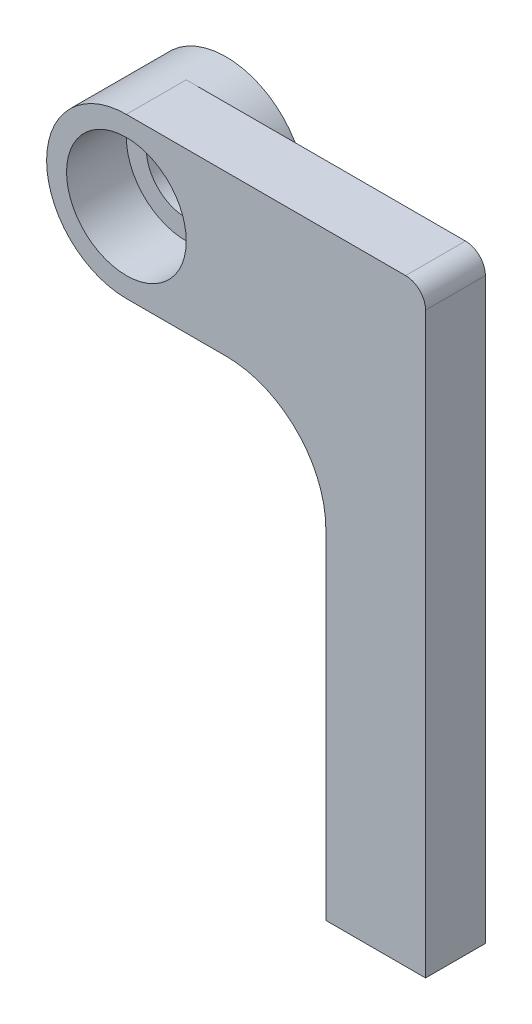
SolidWorks part; units mm, degrees
ref_plane "Front Plane" through (0, 0, 0) normal (0, 0, 1) x (1, 0, 0)
ref_plane "Top Plane" through (0, 0, 0) normal (0, 1, 0) x (1, 0, 0)
ref_plane "Right Plane" through (0, 0, 0) normal (1, 0, 0) x (0, 0, -1)
sketch "Sketch1" plane through (0, 0, 0) normal (0, 0, 1) x (1, 0, 0)
  line L1 (0, -4) -> (10, -4)
  line L3 (0, 4) -> (10, 4)
  line L6 (10, 4) -> (15, 4)
  line L7 (10, -4) -> (10, -26)
  line L8 (10, -26) -> (15, -26)
  line L9 (15, 4) -> (15, -26)
  arc A0 (0, 4) -> (0, -4) centre (0, 0) ccw
  circle A1 centre (0, 0) radius 2
  dimension "D1" = 8
  dimension "D2" = 4
  dimension "D4" = 5
  dimension "D3" = 10
  dimension "D5" = 30
extrude "Boss-Extrude1" add sketch "Sketch1" along normal blind 3 contours L3 L6 L9 L8 L7 L1 A0
sketch "Sketch2" plane through (0, 0, 0) normal (0, 0, -1) x (-1, 0, 0)
  circle A0 centre (0, 0) radius 3
extrude "Cut-Extrude1" cut sketch "Sketch2" against normal blind 5
fillet "Fillet1" radius 5 1 edges at (10, -4, 1.5)
fillet "Fillet3" radius 1 1 edges at (15, 4, 1.5)
sketch "Sketch4" plane through (0, 0, 0) normal (0, 0, -1) x (-1, 0, 0)
  circle A1 centre (0, 0) radius 2
  circle A2 centre (0, 0) radius 4
extrude "Boss-Extrude2" add sketch "Sketch4" along normal blind 2
